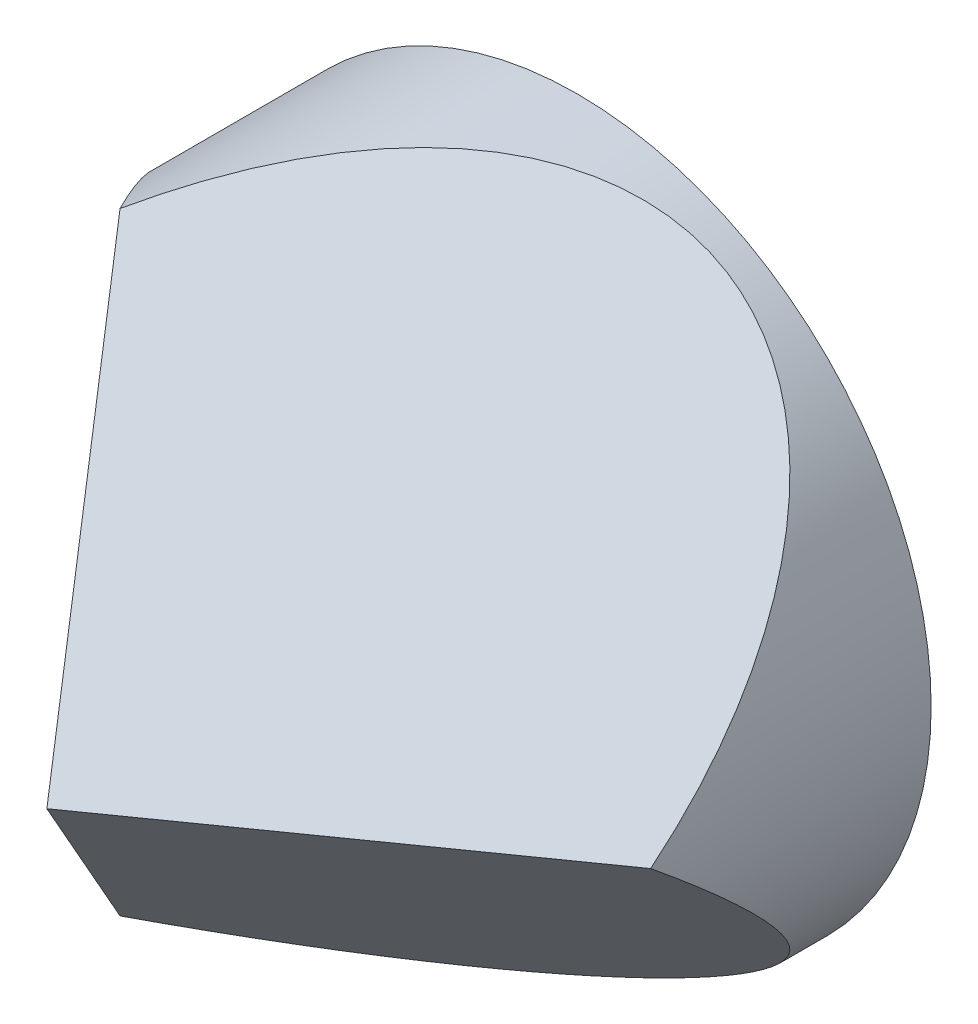
SolidWorks part; units mm, degrees
ref_plane "前视基准面" through (0, 0, 0) normal (0, 0, 1) x (1, 0, 0)
ref_plane "上视基准面" through (0, 0, 0) normal (0, 1, 0) x (1, 0, 0)
ref_plane "右视基准面" through (0, 0, 0) normal (1, 0, 0) x (0, 0, -1)
sketch "草图1" plane through (0, 0, 0) normal (0, 0, 1) x (1, 0, 0)
  circle A0 centre (0, 0) radius 19
  dimension "D1" = 38
extrude "凸台-拉伸1" add sketch "草图1" along normal blind 28.5
sketch "草图2" plane through (0, 0, 0) normal (0, 1, 0) x (1, 0, 0)
  line L0 (0, 0) -> (0, -28.5) construction
  line L1 (-19, -28.5) -> (19, -28.5) construction
  line L2 (0, -28.5) -> (-22.9678, 3.9746)
  line L3 (-22.9678, 3.9746) -> (-22.9678, -37.5189)
  line L4 (-22.9678, -37.5189) -> (0, -37.5189)
  line L5 (0, -37.5189) -> (0, -28.5)
  line L6 (19, 0) -> (-19, 0) construction
  dimension "D1" = 54.73
extrude "切除-拉伸1" cut sketch "草图2" against normal mid plane 49
sketch "草图3" plane through (0, 0, 28.5) normal (0, 0, 1) x (1, 0, 0)
  line L0 (0, 0) -> (16.7186, 0)
  line L1 (0, 0) -> (8.0189, 13.8892)
  line L2 (0, 0) -> (8.0629, -13.9654)
  dimension "D1" = 60
  dimension "D2" = 60
ref_plane "基准面1" through (0, 0, 0) normal (0.866, -0.5, 0) x (0.5, 0.866, 0)
ref_plane "基准面2" through (0, 0, 0) normal (-0.866, -0.5, 0) x (0.5, -0.866, 0)
sketch "草图4" plane through (0, 0, 0) normal (0.866, -0.5, 0) x (0.5, 0.866, 0)
  line L0 (0, 0) -> (0, 22.6417) construction
  line L2 (0, 28.5) -> (68.2544, -68.0063)
  line L3 (0, 28.5) -> (8.3593, 28.5) construction
  line L5 (68.2544, -68.0063) -> (68.2544, 39.7943)
  line L6 (68.2544, 39.7943) -> (0, 39.7943)
  line L7 (0, 39.7943) -> (0, 28.5)
  line L8 (-19, 0) -> (19, 0) construction
  dimension "D1" = 54.73
extrude "切除-拉伸2" cut sketch "草图4" along normal mid plane 74
sketch "草图5" plane through (0, 0, 0) normal (-0.866, -0.5, 0) x (0.5, -0.866, 0)
  line L0 (0, 28.5) -> (25.8693, -8.0772)
  line L1 (0, 28.5) -> (16.1259, 28.5) construction
  line L2 (25.8693, -8.0772) -> (25.8693, 34.997)
  line L3 (25.8693, 34.997) -> (-0.9362, 34.997)
  line L4 (-0.9362, 34.997) -> (0, 28.5)
  line L5 (-19, 0) -> (19, 0) construction
  dimension "D1" = 54.73
extrude "切除-拉伸3" cut sketch "草图5" against normal mid plane 57
